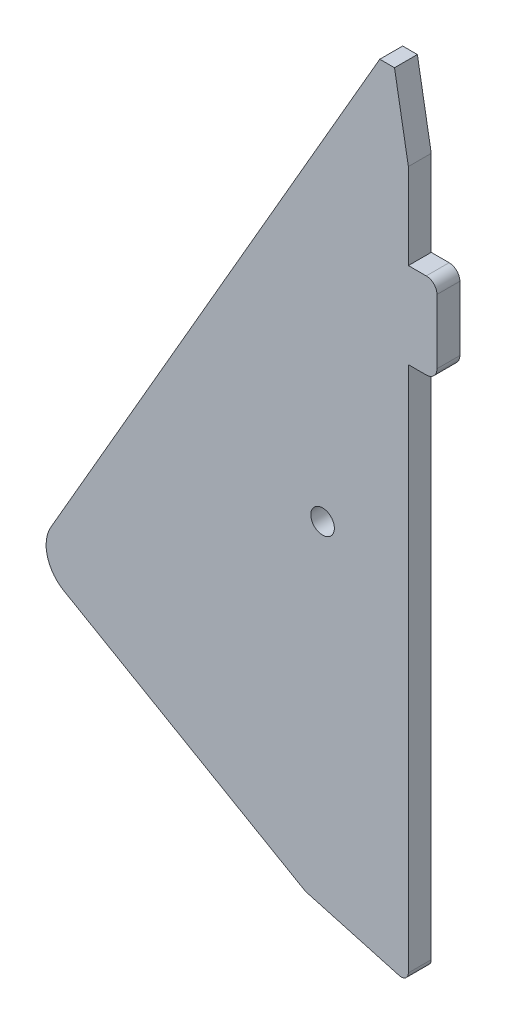
SolidWorks part; units mm, degrees
material "Acrylic (Medium-high impact)"
ref_plane "Front Plane" through (0, 0, 0) normal (0, 0, 1) x (1, 0, 0)
ref_plane "Top Plane" through (0, 0, 0) normal (0, 1, 0) x (1, 0, 0)
ref_plane "Right Plane" through (0, 0, 0) normal (1, 0, 0) x (0, 0, -1)
sketch "Sketch1" plane through (0, 0, 0) normal (0, 0, 1) x (1, 0, 0)
  line L0 (18.8841, -7.966) -> (32.8841, 16.2827) construction
  line L1404 (1.8301, -31.5045) -> (35.6051, -51.0045)
  line L1432 (18.8841, -7.966) -> (21.5342, -9.496) construction
  line L1433 (21.5342, -9.496) -> (35.5342, 14.7527) construction
  line L1434 (35.5342, 14.7527) -> (32.8841, 16.2827) construction
  line L1462 (46, 55) -> (48.0604, 55)
  line L1463 (50, 44) -> (48.0604, 55)
  line L1484 (35.6051, -51.0045) -> (48.7325, -54.6482)
  line L1485 (50, 44) -> (50, -53.6846)
  line L1486 (0, -24.6743) -> (46, 55)
  circle A0 centre (38, -5) radius 1.65
  arc A1 (0, -24.6743) -> (1.8301, -31.5045) centre (4.3301, -27.1743) ccw
  arc A7 (48.7325, -54.6482) -> (50, -53.6846) centre (49, -53.6846) ccw
  dimension "D1" = 3.3
extrude "Boss-Extrude1" add sketch "Sketch1" along normal blind 3.2
sketch "Sketch2" plane through (0, 0, 3.2) normal (0, 0, 1) x (1, 0, 0)
  line L0 (50, -53.6846) -> (50, 44) construction
  line L1 (50, 32) -> (54, 32)
  line L2 (50, 32) -> (50, 20)
  line L3 (50, 20) -> (54, 20)
  line L4 (54, 32) -> (54, 20)
  dimension "D1" = 4
  dimension "D2" = 12
  dimension "D3" = 12
extrude "Boss-Extrude2" add sketch "Sketch2" against normal up to surface (3.2 mm away) up to face at (34.8816, -7.7762, 0)
fillet "Fillet1" radius 1.5 2 edges at (54, 32, 1.6) (54, 20, 1.6)
